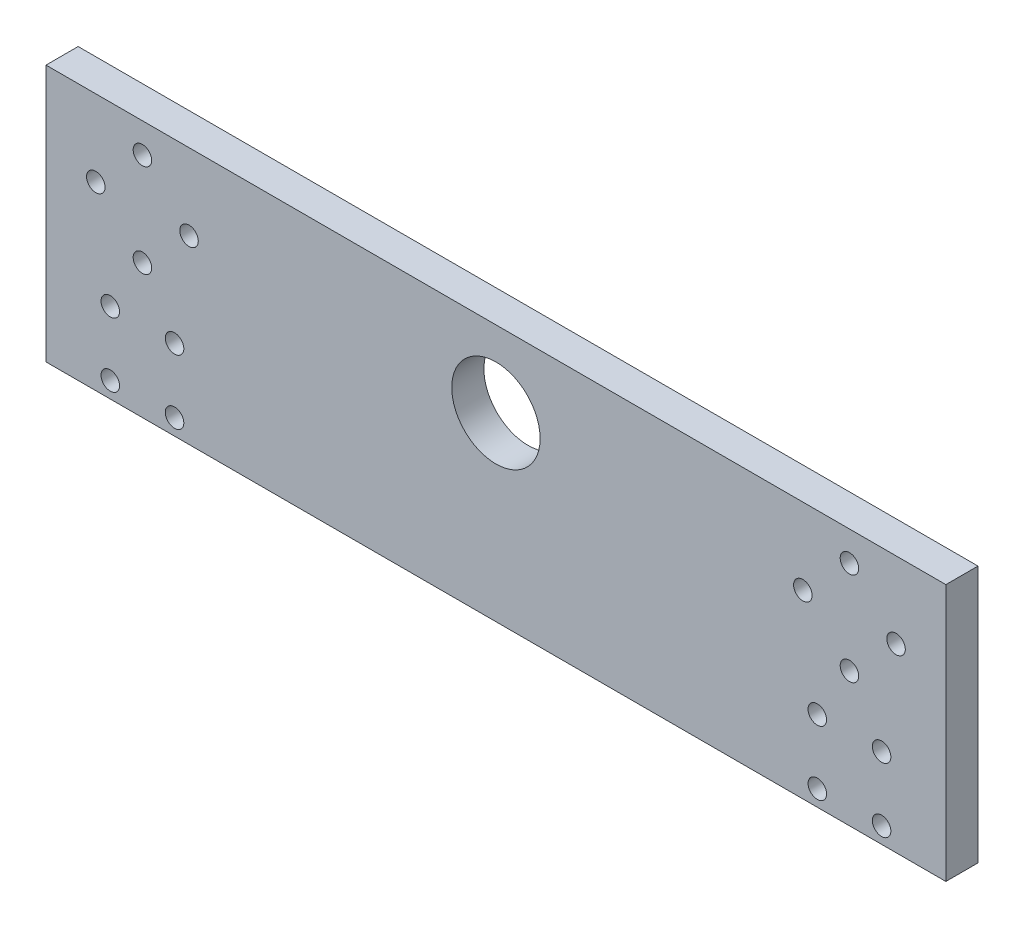
SolidWorks part; units mm, degrees
ref_plane "Front Plane" through (0, 0, 0) normal (0, 0, 1) x (1, 0, 0)
ref_plane "Top Plane" through (0, 0, 0) normal (0, 1, 0) x (1, 0, 0)
ref_plane "Right Plane" through (0, 0, 0) normal (1, 0, 0) x (0, 0, -1)
sketch "Sketch1" plane through (0, 0, 0) normal (0, 0, 1) x (1, 0, 0)
  line L0 (69.85, 0) -> (0, 0) construction
  line L1 (-88.9, 15.0812) -> (88.9, 15.0812)
  line L2 (-88.9, 15.0812) -> (-88.9, -35.7188)
  line L3 (-88.9, -35.7188) -> (88.9, -35.7188)
  line L4 (88.9, 15.0812) -> (88.9, -35.7188)
  line L5 (0, 0) -> (-69.85, 0) construction
  line L6 (0, 15.0812) -> (0, 8.7312) construction
  line L7 (-76.2, 0) -> (-88.9, 0) construction
  line L8 (76.2, 0) -> (88.9, 0) construction
  line L9 (-69.85, -9.2075) -> (-69.85, -19.8438) construction
  line L10 (60.6425, 0) -> (69.85, -9.2075) construction
  line L11 (69.85, -9.2075) -> (79.0575, 0) construction
  line L12 (79.0575, 0) -> (69.85, 9.2075) construction
  line L13 (69.85, 9.2075) -> (60.6425, 0) construction
  line L14 (-79.0575, 0) -> (-69.85, -9.2075) construction
  line L15 (-69.85, -9.2075) -> (-60.6425, 0) construction
  line L16 (-60.6425, 0) -> (-69.85, 9.2075) construction
  line L17 (-69.85, 9.2075) -> (-79.0575, 0) construction
  line L18 (-76.2, -19.8438) -> (-63.5, -19.8438) construction
  line L19 (-76.2, -19.8438) -> (-76.2, -32.5438) construction
  line L20 (-76.2, -32.5438) -> (-63.5, -32.5438) construction
  line L21 (-63.5, -19.8438) -> (-63.5, -32.5438) construction
  line L22 (63.5, -19.8438) -> (76.2, -19.8438) construction
  line L23 (63.5, -19.8438) -> (63.5, -32.5438) construction
  line L24 (63.5, -32.5438) -> (76.2, -32.5438) construction
  line L25 (76.2, -19.8438) -> (76.2, -32.5438) construction
  line L26 (69.85, -9.2075) -> (69.85, -19.8438) construction
  circle A0 centre (0, 0) radius 8.7312
  circle A1 centre (69.85, 0) radius 6.35 construction
  circle A2 centre (-69.85, 0) radius 6.35 construction
  circle A3 centre (-79.0575, 0) radius 1.8288
  circle A4 centre (-60.6425, 0) radius 1.8288
  circle A5 centre (60.6425, 0) radius 1.8288
  circle A6 centre (79.0575, 0) radius 1.8288
  circle A7 centre (-69.85, 0) radius 12.065 construction
  circle A8 centre (69.85, 9.2075) radius 1.8288
  circle A9 centre (69.85, -9.2075) radius 1.8288
  circle A10 centre (-69.85, 9.2075) radius 1.8288
  circle A11 centre (-69.85, -9.2075) radius 1.8288
  circle A12 centre (-76.2, -19.8438) radius 1.8288
  circle A13 centre (-63.5, -19.8438) radius 1.8288
  circle A14 centre (-63.5, -32.5438) radius 1.8288
  circle A15 centre (-76.2, -32.5438) radius 1.8288
  circle A16 centre (63.5, -19.8438) radius 1.8288
  circle A17 centre (76.2, -19.8438) radius 1.8288
  circle A18 centre (76.2, -32.5438) radius 1.8288
  circle A19 centre (63.5, -32.5438) radius 1.8288
  dimension "D1" = 17.4625
  dimension "D4" = 12.7
  dimension "D7" = 3.6576
  dimension "D8" = 24.13
  dimension "D10" = 3.6576
  dimension "D2" = 69.85
  dimension "D3" = 50.8
  dimension "D5" = 6.35
  dimension "D6" = 12.7
  dimension "D9" = 9.2075
  dimension "D11" = 9.2075
  dimension "D12" = 12.7
  dimension "D13" = 3.175
  dimension "D14" = 3.175
extrude "Boss-Extrude1" add sketch "Sketch1" along normal blind 6.35
